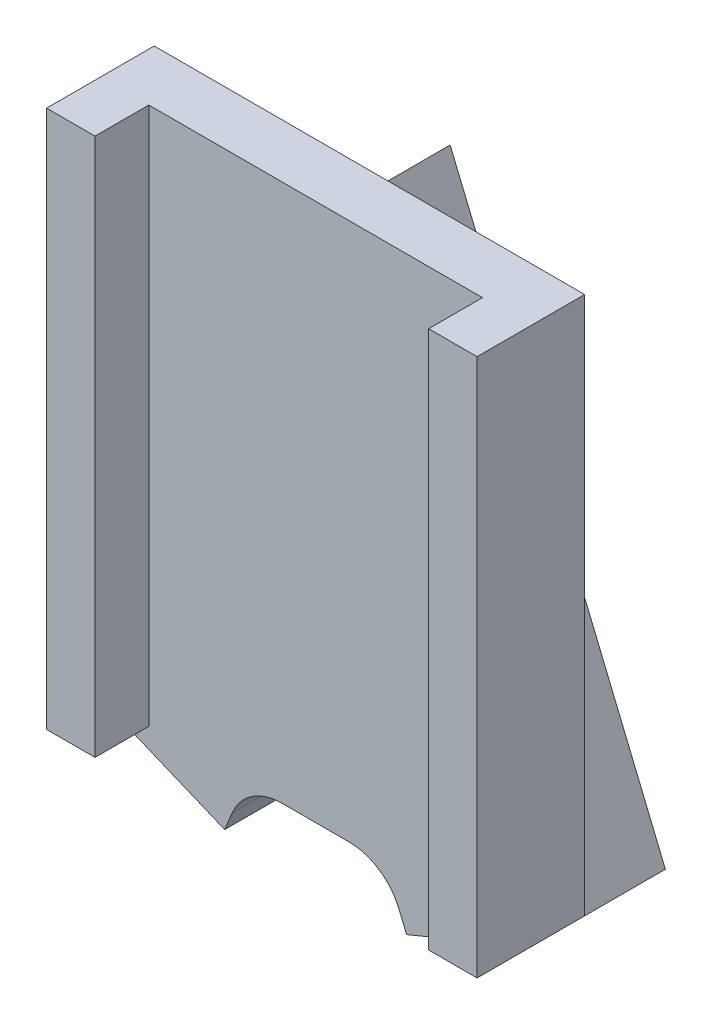
SolidWorks part; units mm, degrees
material "PA Type 6"
ref_plane "Ebene vorne" through (0, 0, 0) normal (0, 0, 1) x (1, 0, 0)
ref_plane "Ebene oben" through (0, 0, 0) normal (0, 1, 0) x (1, 0, 0)
ref_plane "Ebene rechts" through (0, 0, 0) normal (1, 0, 0) x (0, 0, -1)
sketch "Sketch1" plane through (0, 0, 0) normal (0, 0, 1) x (1, 0, 0)
  line L1 (0, 0) -> (8, 0)
  line L2 (0, 0) -> (0, -10)
  line L3 (0, -10) -> (8, -10)
  line L4 (8, 0) -> (8, -10)
extrude "Boss-Extrude1" add sketch "Sketch1" along normal blind 2
sketch "Sketch2" plane through (0, 0, 2) normal (0, 0, 1) x (1, 0, 0)
  line L0 (8, 0) -> (0, 0) construction
  line L1 (0.9, 0) -> (7.1, 0)
  line L2 (0.9, 0) -> (0.9, -10)
  line L3 (0.9, -10) -> (7.1, -10)
  line L4 (7.1, 0) -> (7.1, -10)
  line L5 (0, -10) -> (8, -10) construction
  line L6 (0, 0) -> (0, -10) construction
  line L7 (8, -10) -> (8, 0) construction
  dimension "D1" = 0.9
  dimension "D2" = 0.9
  dimension "D3" = 6.2
extrude "Cut-Extrude1" cut sketch "Sketch2" against normal blind 1
sketch "Sketch3" plane through (0, 0, 0) normal (0, 0, -1) x (-1, 0, 0)
  line L0 (-8, -10) -> (-4, -0.3431)
  line L1 (-8, -10) -> (-5.6903, -10.9567)
  line L4 (-4, 0) -> (-4, -10) construction
  line L5 (-8, 0) -> (0, 0) construction
  line L6 (0, -10) -> (-8, -10) construction
  line L7 (-8, -5) -> (0, -5) construction
  line L8 (-8, -10) -> (-8, 0) construction
  line L9 (0, 0) -> (0, -10) construction
  line L10 (0, -10) -> (-4, -0.3431)
  line L11 (-4, -6.876) -> (-5.6903, -10.9567)
  line L12 (0, -10) -> (-2.3097, -10.9567)
  line L13 (-2.3097, -10.9567) -> (-4, -6.876)
  dimension "D1" = 2.5
  dimension "D2" = 2.5
  dimension "D3" = 45
extrude "Boss-Extrude2" add sketch "Sketch3" along normal blind 1.5 and the other way blind 1
hole_wizard "M1x0.2 Tapped Hole1" positions "Sketch5" profile "Sketch4" tap size "M1x0.2" standard "DIN"
sketch "Sketch5" plane through (-3.5355, -8.5355, 0) normal (-0.3827, -0.9239, 0) x (-0.9239, 0.3827, 0)
  line L0 (-5.0768, 1.5) -> (-5.0768, -1) construction
  line L1 (-6.3268, 1.5) -> (-3.8268, 1.5) construction
  line L2 (-6.3268, -1) -> (-3.8268, -1) construction
  line L4 (-6.3268, 0.25) -> (-3.8268, 0.25) construction
  line L5 (-6.3268, -1) -> (-6.3268, 1.5) construction
  line L6 (-3.8268, 0) -> (-3.8268, 1.5) construction
  point P0 (-5.116, 0.25)
sketch "Sketch4" plane through (1.191, -10.4933, -0.25) normal (0, 0, 1) x (0.9239, -0.3827, 0)
  line L0 (0, 0) -> (0, 2.8403)
  line L1 (0, 2.8403) -> (0.4, 2.6)
  line L2 (0.4, 2.6) -> (0.4, 2)
  line L3 (0.4, 2) -> (0.5, 2)
  line L4 (0.5, 2) -> (0.5, 0)
  line L5 (0.5, 0) -> (0, 0)
  line L10 (0, 2.8403) -> (-0.4, 2.6) construction
  line L11 (0, -6.35) -> (0, 107.95) construction
  dimension "Tap Drill Dia." = 0.8
  dimension "Tap Drill Depth" = 2.6
  dimension "Thread Major Dia." = 1
  dimension "Thread Depth" = 2
  dimension "Drill Angle" = 118
hole_wizard "M1 Clearance Hole1" positions "Sketch6" profile "Sketch7" hole size "M1" standard "DIN"
sketch "Sketch6" plane through (4.7071, -11.364, 0) normal (0.3827, -0.9239, 0) x (-0.9239, -0.3827, 0)
  point P0 (-2.3142, 0.25)
  point P19 (0, 0)
sketch "Sketch7" plane through (6.8452, -10.4784, -0.25) normal (0, 0, 1) x (0.9239, 0.3827, 0)
  line L0 (0, 0) -> (0, 5.3004)
  line L1 (0, 5.3004) -> (0.5, 5)
  line L2 (0.5, 5) -> (0.5, 0)
  line L5 (0.5, 0) -> (0, 0)
  line L10 (0, 5.3004) -> (-0.5, 5) construction
  line L11 (0, -6.35) -> (0, 107.95) construction
  dimension "Hole Dia." = 1
  dimension "Hole Depth" = 5
  dimension "Drill Angle" = 118
sketch "Sketch8" plane through (0, 0, -1.5) normal (0, 0, -1) x (-1, 0, 0)
  circle A0 centre (-4, -7.3) radius 0.4
extrude "Cut-Extrude2" cut sketch "Sketch8" against normal blind 1.5
fillet "Fillet2" radius 1 2 edges at (2.706, -10, 0.5) (5.294, -10, 0.5)
